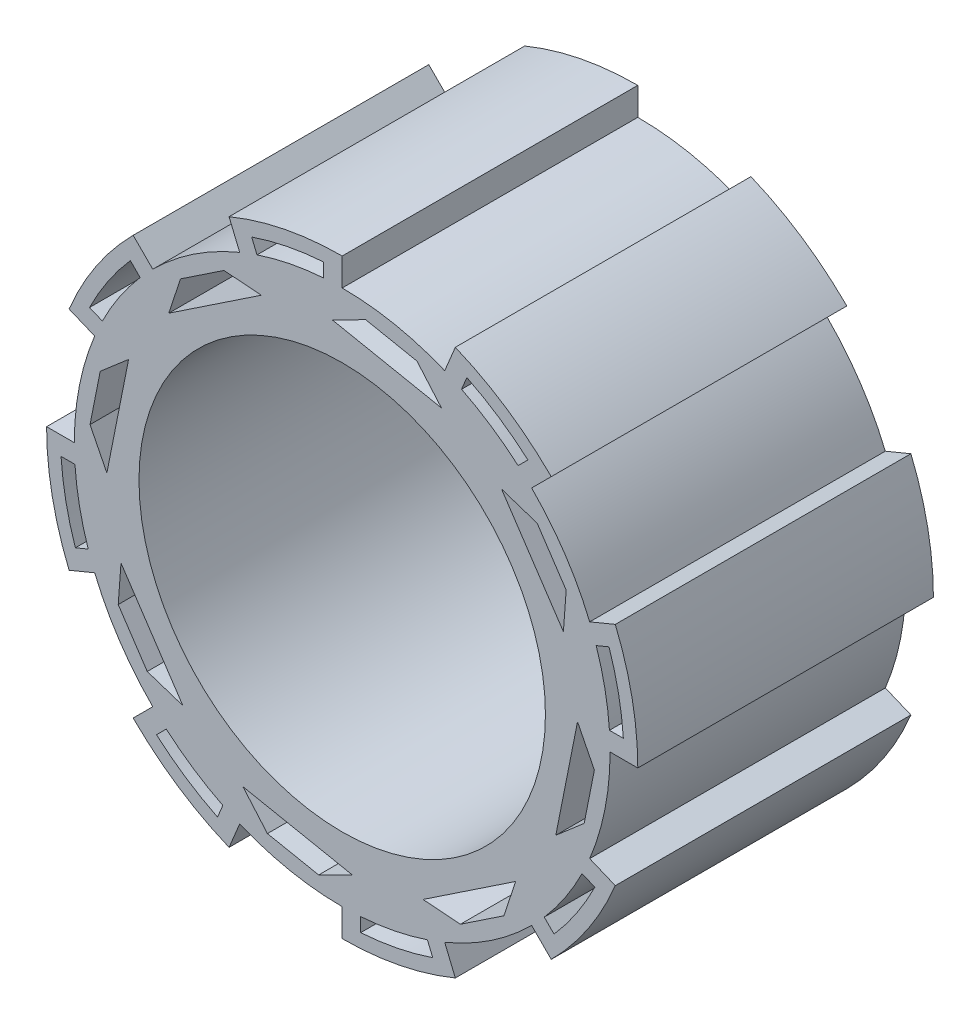
SolidWorks part; units mm, degrees
ref_plane "Front Plane" through (0, 0, 0) normal (0, 0, 1) x (1, 0, 0)
ref_plane "Top Plane" through (0, 0, 0) normal (0, 1, 0) x (1, 0, 0)
ref_plane "Right Plane" through (0, 0, 0) normal (1, 0, 0) x (0, 0, -1)
sketch "Base Drawing " plane through (0, 0, 0) normal (0, 0, 1) x (1, 0, 0)
  line L0 (0, 80) -> (0, -80)
  line L1 (-80, 0) -> (80, 0)
  line L2 (0, 0) -> (-56.5685, 56.5685)
  line L3 (-56.5685, 56.5685) -> (56.5685, -56.5685)
  line L4 (0, 0) -> (56.5685, 56.5685)
  line L5 (56.5685, 56.5685) -> (-56.5685, -56.5685)
  line L14 (0, 0) -> (-25.6326, 61.8826)
  line L15 (0, 0) -> (-30.6147, 73.9104)
  line L16 (-30.6147, 73.9104) -> (30.6147, -73.9104)
  line L17 (25.6326, 61.8826) -> (-25.6326, -61.8826)
  line L18 (-25.6326, -61.8826) -> (-30.6147, -73.9104)
  line L19 (-30.6147, -73.9104) -> (30.6147, 73.9104)
  line L20 (-61.8826, 25.6326) -> (73.9104, -30.6147)
  line L21 (73.9104, -30.6147) -> (-73.9104, 30.6147)
  line L22 (-61.8826, -25.6326) -> (73.9104, 30.6147)
  line L23 (73.9104, 30.6147) -> (-73.9104, -30.6147)
  arc A0 (0, 80) -> (-30.6147, 73.9104) centre (0, 0) ccw
  arc A1 (-27.7445, 66.9813) -> (-51.2652, 51.2652) centre (0, 0) ccw
  arc A2 (56.5685, 56.5685) -> (30.6147, 73.9104) centre (0, 0) ccw
  arc A3 (80, 0) -> (73.9104, 30.6147) centre (0, 0) ccw
  arc A4 (56.5685, -56.5685) -> (73.9104, -30.6147) centre (0, 0) ccw
  arc A5 (0, -80) -> (30.6147, -73.9104) centre (0, 0) ccw
  arc A6 (-56.5685, -56.5685) -> (-30.6147, -73.9104) centre (0, 0) ccw
  arc A7 (-80, 0) -> (-73.9104, -30.6147) centre (0, 0) ccw
  arc A8 (-56.5685, 56.5685) -> (-73.9104, 30.6147) centre (0, 0) ccw
  arc A9 (-66.9813, 27.7445) -> (-72.5, 0) centre (0, 0) ccw
  arc A10 (-66.9813, -27.7445) -> (-51.2652, -51.2652) centre (0, 0) ccw
  arc A11 (-27.7445, -66.9813) -> (0, -72.5) centre (0, 0) ccw
  arc A12 (27.7445, -66.9813) -> (51.2652, -51.2652) centre (0, 0) ccw
  arc A13 (66.9813, -27.7445) -> (72.5, 0) centre (0, 0) ccw
  arc A14 (66.9813, 27.7445) -> (51.2652, 51.2652) centre (0, 0) ccw
  arc A15 (27.7445, 66.9813) -> (0, 72.5) centre (0, 0) ccw
  dimension "D1" = 160
  dimension "D2" = 145
  dimension "D3" = 22.5
  dimension "D4" = 22.5
  dimension "D5" = 22.5
  dimension "D6" = 22.5
  dimension "D7" = 22.5
extrude "Boss-Extrude1" add sketch "Base Drawing " along normal blind 80 contours L0 A0 L16 L15 L14 | L15 A1 L2 L14 | L3 A8 L21 L20 L2 | L21 A9 L1 L20 | L1 A7 L23 L22 | L23 A10 L5 L22 | L5 A6 L19 L18 L17 | L18 A11 L0 L17 | L0 A5 L16 | L16 A12 L3 | L3 A4 L21 L20 | L20 A13 L1 | L1 A3 L23 L22 | L22 A14 L4 | L4 L5 A2 L19 L17 | L19 A15 L0 L17
sketch "Sketch2" plane through (0, 0, 80) normal (0, 0, 1) x (1, 0, 0)
  circle A0 centre (0, 0) radius 55
  dimension "D1" = 110
extrude "Cut-Extrude1" cut sketch "Sketch2" against normal blind 127 and the other way blind 67
sketch "Sketch3" plane through (0, 0, 0) normal (0, 0, -1) x (-1, 0, 0)
  line L0 (51.2652, 51.2652) -> (56.5685, 56.5685)
  line L1 (-53.033, 60.1041) -> (-47.6076, 54.6787)
  line L2 (-51.2652, 51.2652) -> (-56.5685, 56.5685)
  line L3 (-35.2341, 71.9969) -> (-32.3639, 65.0678)
  line L4 (-51.2652, 51.2652) -> (-47.7297, 54.8008)
  line L5 (-56.5685, 56.5685) -> (-53.033, 60.1041)
  line L6 (-47.7297, 54.8008) -> (-53.033, 60.1041)
  line L7 (-27.7445, 66.9813) -> (-30.6147, 73.9104)
  line L8 (-27.7445, 66.9813) -> (-32.3639, 65.0678)
  line L9 (-30.6147, 73.9104) -> (-35.2341, 71.9969)
  line L10 (-32.3639, 65.0678) -> (-35.2341, 71.9969)
  line L11 (-35.2341, 71.9969) -> (-32.2979, 64.9084)
  line L12 (-66.9813, 27.7445) -> (-73.9104, 30.6147)
  line L13 (-66.9813, 27.7445) -> (-68.8947, 23.1252)
  line L14 (-73.9104, 30.6147) -> (-75.8238, 25.9953)
  line L15 (-68.8947, 23.1252) -> (-75.8238, 25.9953)
  line L16 (-72.5, 0) -> (-80, 0)
  line L17 (-72.5, 0) -> (-72.5, 5)
  line L18 (-80, 0) -> (-80, 5)
  line L19 (-72.5, 5) -> (-80, 5)
  line L20 (-75.8238, 25.9953) -> (-68.8947, 23.1252)
  line L21 (-75.8238, 25.9953) -> (-68.7352, 23.0591)
  line L25 (-80, 5) -> (-72.3274, 5)
  line L29 (-66.9813, -27.7445) -> (-73.9104, -30.6147)
  line L30 (-66.9813, -27.7445) -> (-65.0678, -32.3639)
  line L31 (-73.9104, -30.6147) -> (-71.9969, -35.2341)
  line L32 (-65.0678, -32.3639) -> (-71.9969, -35.2341)
  line L33 (-51.2652, -51.2652) -> (-56.5685, -56.5685)
  line L34 (-51.2652, -51.2652) -> (-54.8008, -47.7297)
  line L35 (-56.5685, -56.5685) -> (-60.1041, -53.033)
  line L36 (-54.8008, -47.7297) -> (-60.1041, -53.033)
  line L37 (-60.1041, -53.033) -> (-54.6787, -47.6076)
  line L41 (-68.3635, -33.7291) -> (-64.9084, -32.2979)
  line L45 (-30.6147, -73.9104) -> (-27.7445, -66.9813)
  line L46 (-30.6147, -73.9104) -> (-25.9953, -75.8238)
  line L47 (-27.7445, -66.9813) -> (-23.1252, -68.8947)
  line L48 (-25.9953, -75.8238) -> (-23.1252, -68.8947)
  line L49 (0, -72.5) -> (0, -80)
  line L50 (0, -72.5) -> (-5, -72.5)
  line L51 (0, -80) -> (-5, -80)
  line L52 (-5, -72.5) -> (-5, -80)
  line L53 (-24.4179, -72.0157) -> (-23.0591, -68.7352)
  line L57 (-5, -75.3651) -> (-5, -72.3274)
  line L61 (51.2652, -51.2652) -> (56.5685, -56.5685)
  line L62 (51.2652, -51.2652) -> (47.7297, -54.8008)
  line L63 (56.5685, -56.5685) -> (53.033, -60.1041)
  line L64 (47.7297, -54.8008) -> (53.033, -60.1041)
  line L65 (51.2652, -51.2652) -> (56.5685, -56.5685) construction
  line L66 (27.7445, -66.9813) -> (30.6147, -73.9104)
  line L67 (27.7445, -66.9813) -> (32.3639, -65.0678)
  line L68 (30.6147, -73.9104) -> (35.2341, -71.9969)
  line L69 (32.3639, -65.0678) -> (35.2341, -71.9969)
  line L70 (27.7445, -66.9813) -> (30.6147, -73.9104) construction
  line L71 (33.6039, -68.0615) -> (32.2979, -64.9084)
  line L75 (50.2653, -57.3364) -> (47.6076, -54.6787)
  line L79 (72.5, 0) -> (80, 0)
  line L80 (72.5, 0) -> (72.5, -5)
  line L81 (80, 0) -> (80, -5)
  line L82 (72.5, -5) -> (80, -5)
  line L83 (66.9813, -27.7445) -> (73.9104, -30.6147)
  line L84 (66.9813, -27.7445) -> (68.8947, -23.1252)
  line L85 (73.9104, -30.6147) -> (75.8238, -25.9953)
  line L86 (68.8947, -23.1252) -> (75.8238, -25.9953)
  line L87 (75.8238, -5) -> (72.3274, -5)
  line L91 (70.3826, -23.7415) -> (68.7352, -23.0591)
  line L95 (51.2652, 51.2652) -> (56.5685, 56.5685)
  line L96 (51.2652, 51.2652) -> (54.8008, 47.7297)
  line L97 (56.5685, 56.5685) -> (60.1041, 53.033)
  line L98 (54.8008, 47.7297) -> (60.1041, 53.033)
  line L99 (66.9813, 27.7445) -> (73.9104, 30.6147)
  line L100 (66.9813, 27.7445) -> (65.0678, 32.3639)
  line L101 (73.9104, 30.6147) -> (71.9969, 35.2341)
  line L102 (65.0678, 32.3639) -> (71.9969, 35.2341)
  line L103 (56.1843, 49.1133) -> (54.6787, 47.6076)
  line L115 (66.3364, 32.8894) -> (64.9084, 32.2979)
  line L119 (54.68, 47.6089) -> (54.6774, 47.6063)
  line L120 (65.4316, 32.5146) -> (64.8373, 32.2685)
  line L121 (72.3373, -5) -> (72.3238, -5)
  line L122 (69.253, -23.2736) -> (67.2291, -22.4352)
  line L123 (48.4708, -55.5419) -> (44.4221, -51.4932)
  line L124 (32.9362, -66.4493) -> (30.6147, -60.923)
  line L125 (-5, -74.4641) -> (-5, -60.1041)
  line L126 (-23.9325, -70.8438) -> (-18.526, -57.7914)
  line L127 (-56.2569, -49.1859) -> (-52.4574, -45.3864)
  line L128 (-66.9813, -33.1565) -> (-57.4433, -29.2057)
  line L129 (-74.6687, 5) -> (-65.0678, 5)
  line L130 (-71.0014, 23.9978) -> (-65.0678, 21.54)
  line L131 (-49.2038, 56.2749) -> (-44.0713, 51.1424)
  line L132 (-33.1565, 66.9813) -> (-30.6147, 60.8447)
  line L133 (0, 72.5) -> (0, 80)
  line L134 (0, 72.5) -> (5, 72.5)
  line L135 (0, 80) -> (5, 80)
  line L136 (5, 72.5) -> (5, 80)
  line L137 (27.7445, 66.9813) -> (30.6147, 73.9104)
  line L138 (27.7445, 66.9813) -> (23.1252, 68.8947)
  line L139 (30.6147, 73.9104) -> (25.9953, 75.8238)
  line L140 (23.1252, 68.8947) -> (25.9953, 75.8238)
  line L141 (5, 74.9522) -> (5, 69.1426)
  line L142 (24.1329, 71.3276) -> (21.7386, 65.5472)
  circle A0 centre (0, 0) radius 72.5
  arc A1 (30.6147, -73.9104) -> (56.5685, -56.5685) centre (0, 0) ccw construction
  circle A2 centre (0, 0) radius 76.25
  dimension "D1" = 152.5
  dimension "D2" = 5
  dimension "D3" = 5
  dimension "D4" = 5
  dimension "D5" = 5
  dimension "D6" = 5
  dimension "D7" = 5
  dimension "D8" = 5
  dimension "D9" = 5
  dimension "D10" = 5
  dimension "D11" = 5
  dimension "D12" = 5
  dimension "D13" = 5
  dimension "D14" = 5
  dimension "D15" = 5
  dimension "D16" = 5
  dimension "D17" = 5
extrude "Cut-Extrude2" cut sketch "Sketch3" against normal blind 103 and the other way blind 21 contours L11 A2 L6 L1 A0 | L21 A2 L25 L19 A0 L15 | L32 A2 L37 L36 A0 L41 | L48 A2 L52 L57 A0 L53 | L69 A2 L75 L64 A0 L71 | L86 A2 L82 L87 A0 L91 | L102 A2 L98 L103 A0 L115 | L140 A2 L136 L141 A0 L142
sketch "Sketch5" plane through (0, 0, 0) normal (0, 0, -1) x (-1, 0, 0)
  line L0 (-27.7445, 66.9813) -> (51.2652, 51.2652)
  line L1 (66.9813, 27.7445) -> (51.2652, -51.2652)
  line L2 (27.7445, -66.9813) -> (-51.2652, -51.2652)
  line L3 (-66.9813, -27.7445) -> (-51.2652, 51.2652)
  line L4 (27.7445, 66.9813) -> (72.5, 0)
  line L5 (66.9813, -27.7445) -> (0, -72.5)
  line L6 (-27.7445, -66.9813) -> (-72.5, 0)
  line L7 (-66.9813, 27.7445) -> (0, 72.5)
  line L8 (-66.9813, 27.7445) -> (-72.5, 0)
  line L9 (-51.2652, 51.2652) -> (-27.7445, 66.9813)
  line L10 (0, 72.5) -> (27.7445, 66.9813)
  line L11 (51.2652, 51.2652) -> (66.9813, 27.7445)
  line L12 (72.5, 0) -> (66.9813, -27.7445)
  line L13 (51.2652, -51.2652) -> (27.7445, -66.9813)
  line L14 (0, -72.5) -> (-27.7445, -66.9813)
  line L15 (-51.2652, -51.2652) -> (-66.9813, -27.7445)
  line L16 (-27.7445, 66.9813) -> (0, 72.5)
  line L17 (27.7445, 66.9813) -> (51.2652, 51.2652)
  line L18 (66.9813, 27.7445) -> (72.5, 0)
  line L19 (66.9813, -27.7445) -> (51.2652, -51.2652)
  line L20 (27.7445, -66.9813) -> (0, -72.5)
  line L21 (-27.7445, -66.9813) -> (-51.2652, -51.2652)
  line L22 (-66.9813, -27.7445) -> (-72.5, 0)
  line L23 (-66.9813, 27.7445) -> (-51.2652, 51.2652)
  line L24 (-27.7445, 66.9813) -> (-12.7293, 63.9945)
  line L25 (-12.7293, 63.9945) -> (-20.2369, 65.4879)
  line L26 (-20.2369, 65.4879) -> (-33.4906, 50.1223)
  line L27 (-12.7293, 63.9945) -> (0, 72.5)
  line L28 (-6.3647, 68.2473) -> (11.7603, 59.1233)
  line L29 (-20.2369, 65.4879) -> (-6.3647, 68.2473)
  line L30 (-26.8638, 57.8051) -> (2.6978, 63.6853)
  line L31 (-66.9813, 27.7445) -> (-54.252, 36.25)
  line L32 (-54.252, 36.25) -> (-51.2652, 51.2652)
  line L33 (-52.7586, 43.7576) -> (-33.4906, 50.1223)
  line L34 (-66.9813, 27.7445) -> (-54.252, 36.25)
  line L35 (-60.6166, 31.9973) -> (-59.1233, 11.7603)
  line L36 (-60.6166, 31.9973) -> (-52.7586, 43.7576)
  line L38 (-59.8699, 21.8788) -> (-43.1246, 46.9399)
  line L39 (-72.5, 0) -> (-63.9945, -12.7293)
  line L40 (-63.9945, -12.7293) -> (-66.9813, -27.7445)
  line L41 (-68.2473, -6.3647) -> (-59.1233, 11.7603)
  line L42 (-66.9813, -27.7445) -> (-63.9945, -12.7293)
  line L43 (-65.4879, -20.2369) -> (-50.1223, -33.4906)
  line L45 (-68.2473, -6.3647) -> (-65.4879, -20.2369)
  line L46 (-63.9945, -12.7293) -> (-59.1233, 11.7603)
  line L47 (-63.6853, 2.6978) -> (-57.8051, -26.8638)
  line L48 (34.4094, 51.4973) -> (39.5049, 59.1233)
  line L49 (39.5049, 59.1233) -> (36.25, 54.252)
  line L50 (36.25, 54.252) -> (27.7445, 66.9813)
  line L51 (36.25, 54.252) -> (51.2652, 51.2652)
  line L52 (43.7576, 52.7586) -> (31.9973, 60.6166)
  line L53 (31.9973, 60.6166) -> (11.7603, 59.1233)
  line L54 (43.7576, 52.7586) -> (50.1223, 33.4906)
  line L55 (46.9399, 43.1246) -> (21.8788, 59.8699)
  line L56 (69.7406, 13.8723) -> (63.9945, 12.7293)
  line L57 (63.9945, 12.7293) -> (66.9813, 27.7445)
  line L58 (63.9945, 12.7293) -> (72.5, 0)
  line L59 (68.2473, 6.3647) -> (65.4879, 20.2369)
  line L60 (65.4879, 20.2369) -> (50.1223, 33.4906)
  line L61 (68.2473, 6.3647) -> (59.1233, -11.7603)
  line L62 (63.6853, -2.6978) -> (57.8051, 26.8638)
  line L63 (59.1233, -39.5049) -> (54.252, -36.25)
  line L64 (54.252, -36.25) -> (66.9813, -27.7445)
  line L65 (54.252, -36.25) -> (51.2652, -51.2652)
  line L66 (52.7586, -43.7576) -> (60.6166, -31.9973)
  line L67 (60.6166, -31.9973) -> (59.1233, -11.7603)
  line L68 (52.7586, -43.7576) -> (33.4906, -50.1223)
  line L69 (43.1246, -46.9399) -> (59.8699, -21.8788)
  line L70 (13.8723, -69.7406) -> (12.7293, -63.9945)
  line L71 (0, -72.5) -> (12.7293, -63.9945)
  line L72 (27.7445, -66.9813) -> (12.7293, -63.9945)
  line L73 (6.3647, -68.2473) -> (20.2369, -65.4879)
  line L74 (20.2369, -65.4879) -> (33.4906, -50.1223)
  line L75 (6.3647, -68.2473) -> (-11.7603, -59.1233)
  line L76 (-2.6978, -63.6853) -> (26.8638, -57.8051)
  line L77 (-39.5049, -59.1233) -> (-36.25, -54.252)
  line L78 (-51.2652, -51.2652) -> (-36.25, -54.252)
  line L79 (-27.7445, -66.9813) -> (-36.25, -54.252)
  line L80 (-43.7576, -52.7586) -> (-50.1223, -33.4906)
  line L81 (-31.9973, -60.6166) -> (-11.7603, -59.1233)
  line L82 (-43.7576, -52.7586) -> (-31.9973, -60.6166)
  line L83 (-21.8788, -59.8699) -> (-46.9399, -43.1246)
extrude "Cut-Extrude3" cut sketch "Sketch5" against normal blind 105 and the other way blind 36 contours L35 L38 L3 L34 | L3 L38 L7 | L7 L38 L33 L3 | L36 L34 L3 | L26 L30 L7 L24 | L29 L24 L7 | L0 L30 L28 L7 | L7 L30 L0 | L55 L0 L50 L53 | L55 L48 L0 | L55 L54 L0 L4 | L0 L52 L48 | L48 L52 L50 | L55 L4 L48 | L62 L61 L4 L1 | L62 L1 L4 | L62 L4 L57 L60 | L56 L59 L57 | L4 L59 L56 | L1 L66 L63 | L63 L66 L64 | L69 L1 L64 L67 | L69 L5 L1 | L69 L68 L1 L5 | L76 L75 L5 L2 | L5 L73 L70 | L70 L73 L72 | L76 L5 L72 L74 | L76 L2 L5 | L6 L83 L80 L2 | L2 L82 L77 | L77 L82 L79 | L81 L83 L2 L79 | L2 L83 L6 | L47 L41 L6 L3 | L6 L45 L42 | L47 L6 L42 L43 | L47 L3 L6
